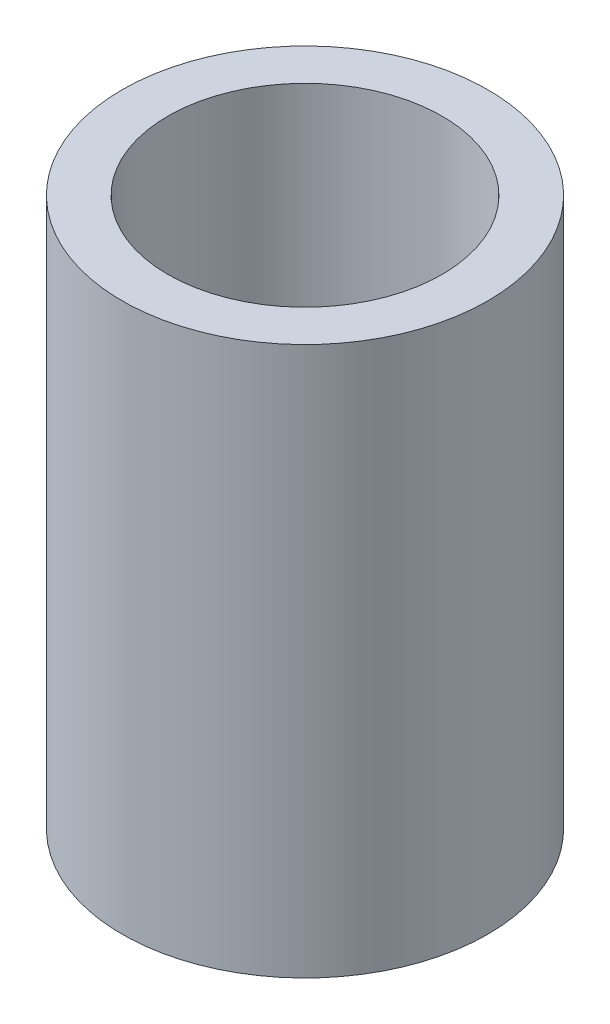
SolidWorks part; units mm, degrees
ref_plane "Front Plane" through (0, 0, 0) normal (0, 0, 1) x (1, 0, 0)
ref_plane "Top Plane" through (0, 0, 0) normal (0, 1, 0) x (1, 0, 0)
ref_plane "Right Plane" through (0, 0, 0) normal (1, 0, 0) x (0, 0, -1)
sketch "Sketch3" plane through (0, 0, 0) normal (0, 1, 0) x (1, 0, 0)
  circle A0 centre (0, 0) radius 3
  dimension "D1" = 6
extrude "Extrude-Thin1" add sketch "Sketch3" along normal blind 12 thin
